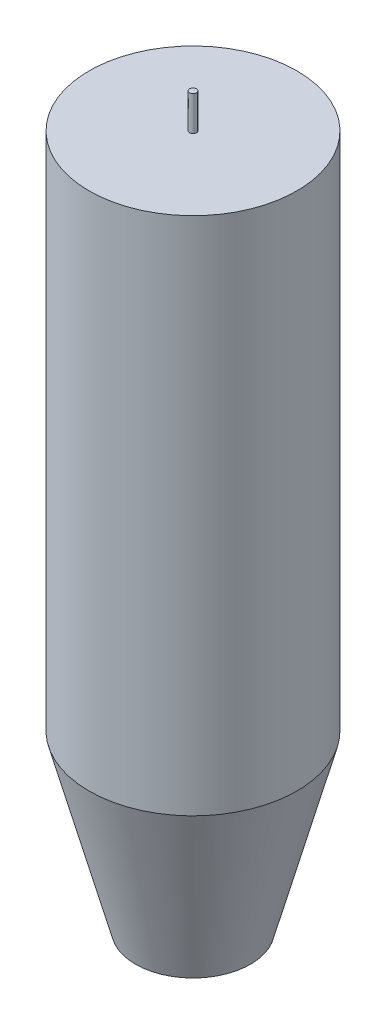
SolidWorks part; units mm, degrees
ref_plane "Front Plane" through (0, 0, 0) normal (0, 0, 1) x (1, 0, 0)
ref_plane "Top Plane" through (0, 0, 0) normal (0, 1, 0) x (1, 0, 0)
ref_plane "Right Plane" through (0, 0, 0) normal (1, 0, 0) x (0, 0, -1)
sketch "Sketch2" plane through (0, 0, 0) normal (0, 1, 0) x (1, 0, 0)
  circle A0 centre (0, 0) radius 15
  dimension "D1" = 30
extrude "Boss-Extrude1" add sketch "Sketch2" along normal blind 100 contours A0
chamfer "Chamfer1" distance 25 angle 15 1 edges at (0, 0, 15)
sketch "Sketch3" plane through (0, 100, 0) normal (0, 1, 0) x (1, 0, 0)
  circle A0 centre (0, 0) radius 0.5
  dimension "D1" = 1
extrude "Boss-Extrude2" add sketch "Sketch3" along normal blind 5
